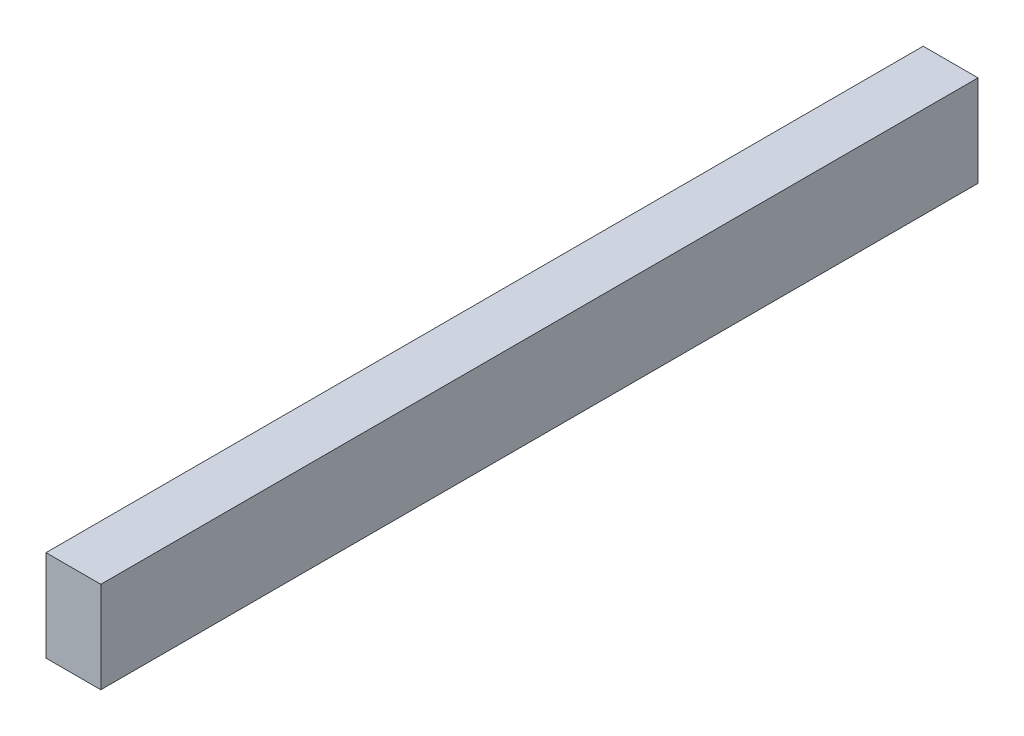
SolidWorks part; units mm, degrees
ref_plane "Front Plane" through (0, 0, 0) normal (0, 0, 1) x (1, 0, 0)
ref_plane "Top Plane" through (0, 0, 0) normal (0, 1, 0) x (1, 0, 0)
ref_plane "Right Plane" through (0, 0, 0) normal (1, 0, 0) x (0, 0, -1)
sketch "Sketch1" plane through (0, 0, 0) normal (0, 0, 1) x (1, 0, 0)
  line L1 (-19.05, -31.75) -> (19.05, -31.75)
  line L2 (-19.05, -31.75) -> (-19.05, 31.75)
  line L3 (-19.05, 31.75) -> (19.05, 31.75)
  line L4 (19.05, -31.75) -> (19.05, 31.75)
  line L5 (-19.05, -31.75) -> (19.05, 31.75) construction
  line L6 (-19.05, 31.75) -> (19.05, -31.75) construction
  point P0 (0, 0)
  dimension "D1" = 38.1
  dimension "D2" = 63.5
extrude "Boss-Extrude1" add sketch "Sketch1" along normal blind 609.6
